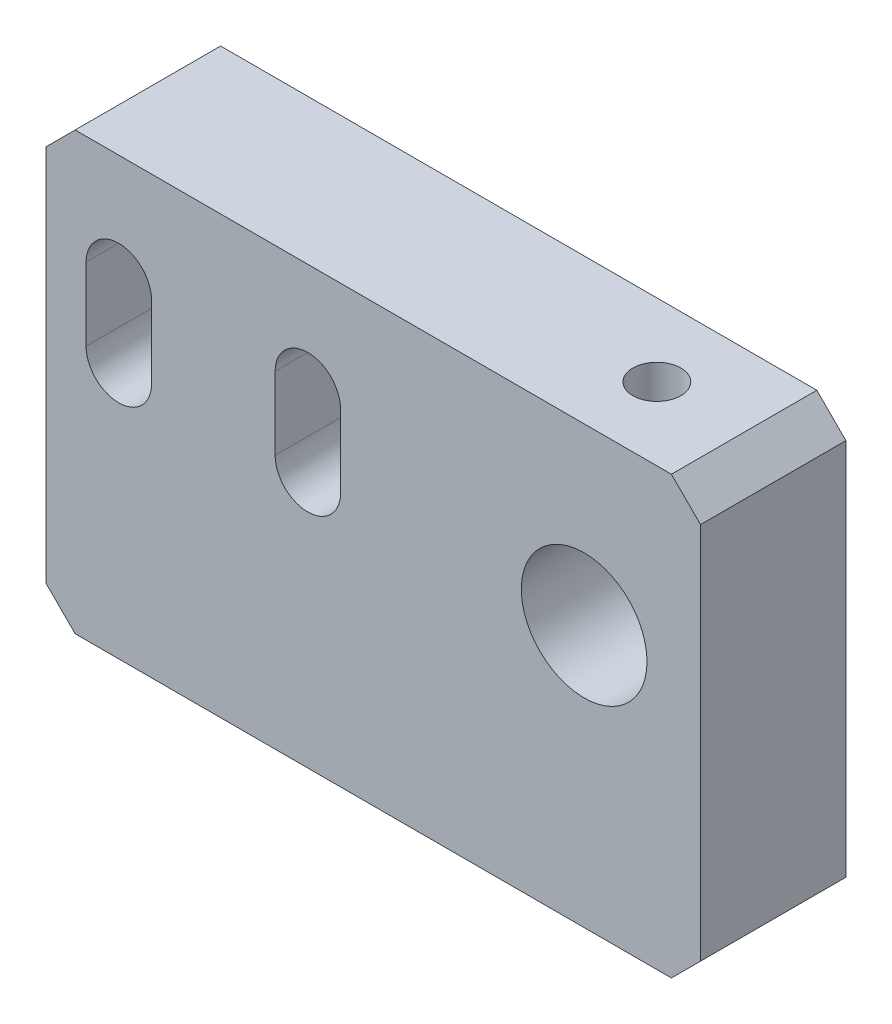
SolidWorks part; units mm, degrees
ref_plane "Front Plane" through (0, 0, 0) normal (0, 0, 1) x (1, 0, 0)
ref_plane "Top Plane" through (0, 0, 0) normal (0, 1, 0) x (1, 0, 0)
ref_plane "Right Plane" through (0, 0, 0) normal (1, 0, 0) x (0, 0, -1)
sketch "Sketch1" plane through (0, 0, 0) normal (0, 0, 1) x (1, 0, 0)
  line L0 (-9.5075, 5) -> (-9.5075, 0) construction
  line L1 (-14.5075, 12.5) -> (30.4925, 12.5)
  line L2 (-14.5075, 12.5) -> (-14.5075, -17.5)
  line L3 (-14.5075, -17.5) -> (30.4925, -17.5)
  line L4 (30.4925, 12.5) -> (30.4925, -17.5)
  line L5 (-7.2575, 5) -> (-7.2575, 0)
  line L6 (-11.7575, 5) -> (-11.7575, 0)
  line L7 (3.4925, 5) -> (3.4925, 0) construction
  line L8 (5.7425, 5) -> (5.7425, 0)
  line L9 (1.2425, 5) -> (1.2425, 0)
  arc A0 (-7.2575, 5) -> (-11.7575, 5) centre (-9.5075, 5) ccw
  arc A1 (-11.7575, 0) -> (-7.2575, 0) centre (-9.5075, 0) ccw
  arc A2 (5.7425, 5) -> (1.2425, 5) centre (3.4925, 5) ccw
  arc A3 (1.2425, 0) -> (5.7425, 0) centre (3.4925, 0) ccw
  circle A4 centre (22.4925, 0.5) radius 4.3221
  point P6 (-9.5075, 2.5)
  point P11 (3.4925, 2.5)
  dimension "D1" = 45
  dimension "D2" = 30
  dimension "D3" = 4.5
  dimension "D4" = 17.5
  dimension "D5" = 22.5
  dimension "D6" = 4.5
  dimension "D7" = 17.5
  dimension "D8" = 22.5
  dimension "D9" = 8
  dimension "D10" = 18
  dimension "D11" = 27
  dimension "D12" = 40
extrude "Boss-Extrude1" add sketch "Sketch1" along normal blind 10
hole_wizard "M4 Tapped Hole1" positions "Sketch2" profile "Sketch3" tap size "M4" standard "ISO"
sketch "Sketch2" plane through (0, 12.5, 0) normal (0, 1, 0) x (1, 0, 0)
  line L0 (30.4925, -10) -> (30.4925, 0) construction
  line L1 (30.4925, -10) -> (-14.5075, -10) construction
  point P0 (22.4925, -5)
  dimension "D1" = 8
  dimension "D2" = 5
sketch "Sketch3" plane through (22.4925, 12.5, 5) normal (1, 0, 0) x (0, 0, 1)
  line L0 (0, 0) -> (0, 11.0914)
  line L1 (0, 11.0914) -> (1.65, 10.1)
  line L2 (1.65, 10.1) -> (1.65, 0)
  line L5 (1.65, 0) -> (0, 0)
  line L10 (0, 11.0914) -> (-1.65, 10.1) construction
  line L11 (0, -6.35) -> (0, 107.95) construction
  dimension "Tap Drill Dia." = 3.3
  dimension "Tap Drill Depth" = 10.1
  dimension "Drill Angle" = 118
cosmetic thread "Hole Thread1" parameters "D1"=8, "D2"=4
chamfer "Chamfer2" distance 2 angle 45 4 edges at (-14.5075, 12.5, 5) (30.4925, 12.5, 5) (-14.5075, -17.5, 5) (30.4925, -17.5, 5)
